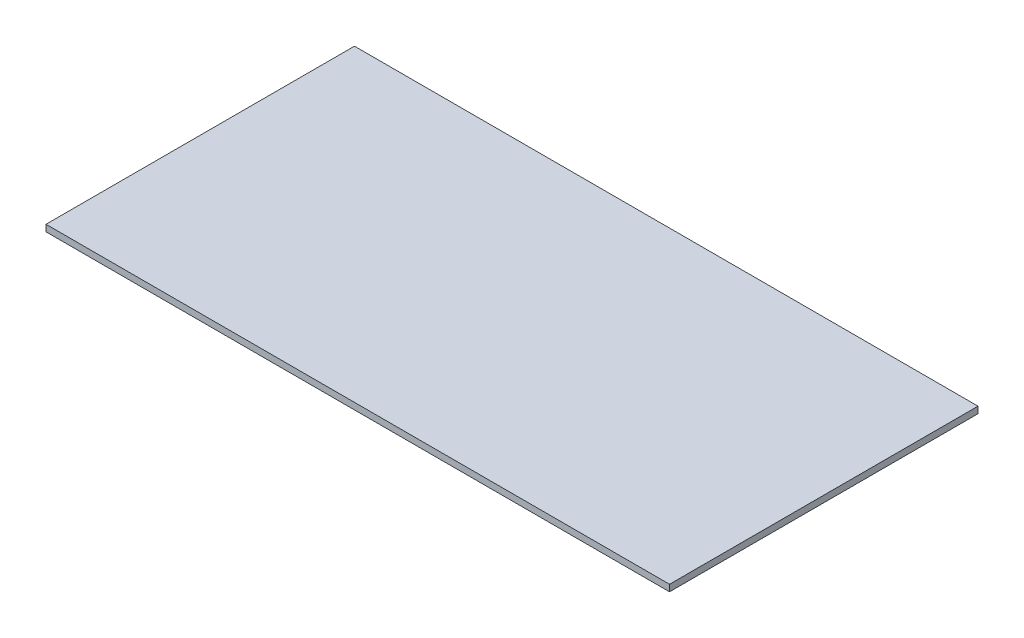
SolidWorks part; units mm, degrees
ref_plane "Front Plane" through (0, 0, 0) normal (0, 0, 1) x (1, 0, 0)
ref_plane "Top Plane" through (0, 0, 0) normal (0, 1, 0) x (1, 0, 0)
ref_plane "Right Plane" through (0, 0, 0) normal (1, 0, 0) x (0, 0, -1)
sketch "Sketch1" plane through (0, 0, 0) normal (0, 1, 0) x (-1, 0, 0)
  line L1 (-142.5, 70.5) -> (142.5, 70.5)
  line L2 (-142.5, 70.5) -> (-142.5, -70.5)
  line L3 (-142.5, -70.5) -> (142.5, -70.5)
  line L4 (142.5, 70.5) -> (142.5, -70.5)
  line L5 (-142.5, 70.5) -> (142.5, -70.5) construction
  line L6 (-142.5, -70.5) -> (142.5, 70.5) construction
  point P0 (0, 0)
  dimension "D1" = 285
  dimension "D2" = 141
extrude "Boss-Extrude1" add sketch "Sketch1" along normal blind 3
